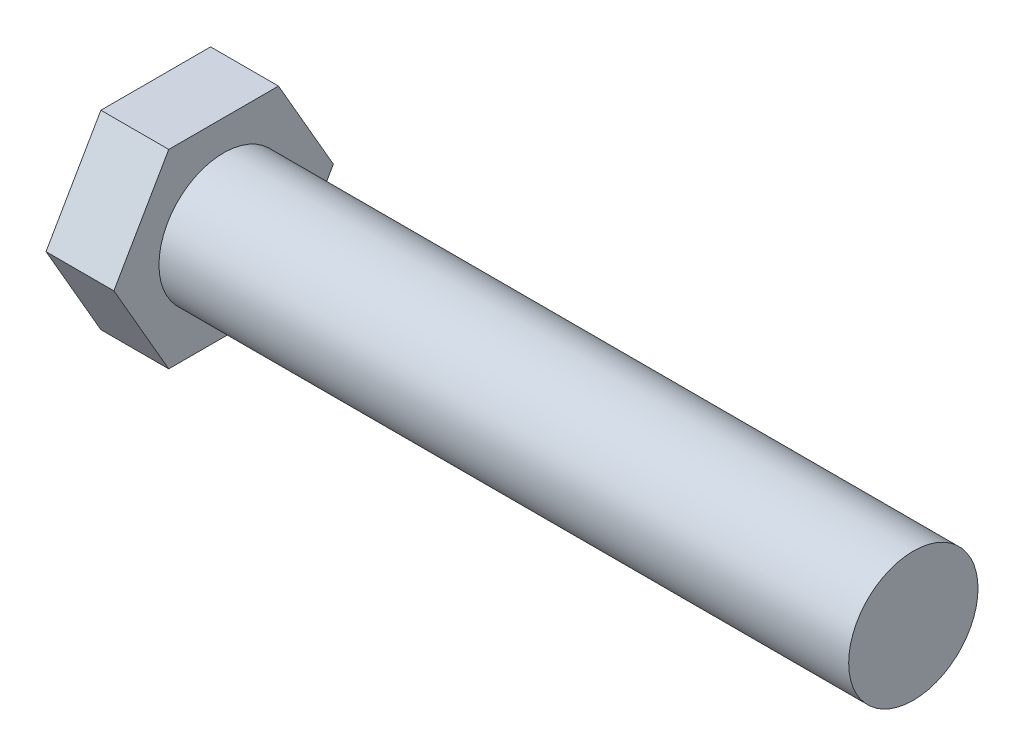
SolidWorks part; units mm, degrees
ref_plane "Front Plane" through (0, 0, 0) normal (0, 0, 1) x (1, 0, 0)
ref_plane "Top Plane" through (0, 0, 0) normal (0, 1, 0) x (1, 0, 0)
ref_plane "Right Plane" through (0, 0, 0) normal (1, 0, 0) x (0, 0, -1)
sketch "Sketch1" plane through (0, 0, 0) normal (1, 0, 0) x (0, 0, -1)
  circle A0 centre (0, 0) radius 4.7625
  dimension "D1" = 9.525
extrude "Boss-Extrude1" add sketch "Sketch1" along normal blind 50.8
sketch "Sketch2" plane through (0, 0, 0) normal (-1, 0, 0) x (0, 0, 1)
  line L1 (8.0829, 0) -> (4.0415, 7)
  line L2 (4.0415, 7) -> (-4.0415, 7)
  line L3 (-4.0415, 7) -> (-8.0829, 0)
  line L4 (-8.0829, 0) -> (-4.0415, -7)
  line L5 (-4.0415, -7) -> (4.0415, -7)
  line L6 (4.0415, -7) -> (8.0829, 0)
  circle A0 centre (0, 0) radius 7 construction
extrude "Boss-Extrude2" add sketch "Sketch2" along normal blind 5
